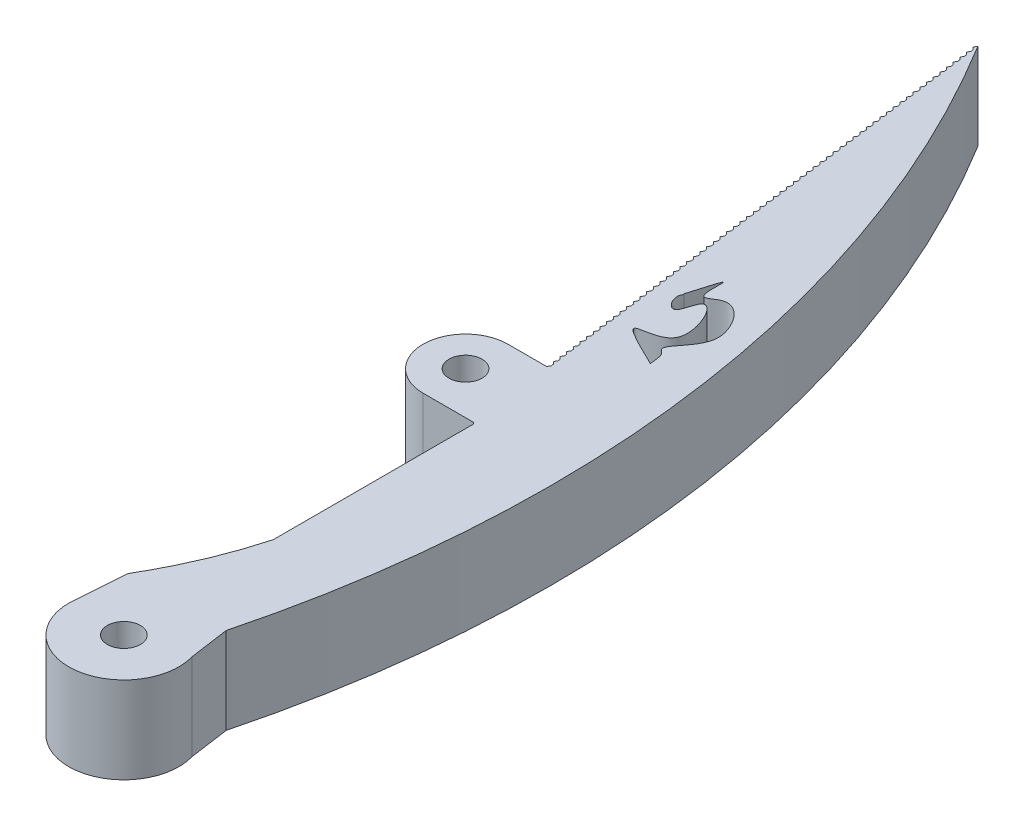
SolidWorks part; units mm, degrees
ref_plane "Front Plane" through (0, 0, 0) normal (0, 0, 1) x (1, 0, 0)
ref_plane "Top Plane" through (0, 0, 0) normal (0, 1, 0) x (1, 0, 0)
ref_plane "Right Plane" through (0, 0, 0) normal (1, 0, 0) x (0, 0, -1)
sketch "Sketch1" plane through (0, 0, 0) normal (0, 1, 0) x (1, 0, 0)
  line L0 (-7.0665, 25.8404) -> (-13.8742, 78.4137)
  line L1 (-7.0665, 38.4137) -> (-7.0665, -14.5937) construction
  line L4 (-2.0665, -1.5863) -> (-1.3548, -6.5863)
  line L5 (-11, -1.5863) -> (-11.3548, -6.5863)
  circle A0 centre (-6.3548, -6.5863) radius 5
  arc A1 (-13.8742, 78.4137) -> (-2.0665, -1.5863) centre (-102.1506, 24.5131) cw
  spline S0 degree 3 poles (-7.0665, 25.8404) (-4.6608, 16.1109) (-5.9719, 6.9687) (-11, -1.5863) knots 0.29583 0.29583 0.29583 0.29583 1 1 1 1
  dimension "D2" = 10
extrude "Boss-Extrude1" add sketch "Sketch1" along normal blind 7.85
sketch "Sketch2" plane through (0, 7.85, 0) normal (0, 1, 0) x (1, 0, 0)
  line L0 (-1.3548, -6.5863) -> (-11.3548, -6.5863) construction
  circle A0 centre (-6.3548, -6.5863) radius 1.5
  dimension "D1" = 3
sketch "Sketch3" plane through (0, 7.85, 0) normal (0, 1, 0) x (1, 0, 0)
  line L0 (-7.0665, 25.8404) -> (-7.2786, 26.0525)
  line L1 (-7.0665, 7.6866) -> (-7.0665, 25.8404) construction
  line L2 (-7.2786, 26.0525) -> (-7.1275, 26.3117)
  line L3 (-7.0665, 25.8404) -> (-7.1275, 26.3117)
  line L4 (-7.0665, 25.8404) -> (-13.8742, 78.4137) construction
  dimension "D1" = 0.3
sketch "Sketch4" plane through (0, 0, 0) normal (0, -1, 0) x (-1, 0, 0)
  line L0 (1.3548, -6.5863) -> (11.3548, -6.5863) construction
  circle A0 centre (6.3548, -6.5863) radius 1.5
  dimension "D1" = 3
extrude "Boss-Extrude9" add sketch "Sketch3" against normal blind 7.5 contours L2 L3 L0
pattern_linear "LPattern1" count 76 spacing 0.7 along (-0.1284, 0, -0.9917) of "Boss-Extrude9"
extrude "Cut-Extrude1" cut sketch "Sketch2" against normal through all contours A0
sketch "Sketch10" plane through (0, 0, 0) normal (0, -1, 0) x (1, 0, 0)
  spline S0 degree 3 poles (-3.7961, -38.6108) (-10.715, -41.9083) (-1.8362, -38.721) (-6.2564, -47.8465) (-6.6902, -42.8482) (-8.1696, -44.9623) (-7.6725, -45.5915) (-7.7718, -45.5603) knots 0 0 0 0 0.43333 0.726209 0.863353 0.989851 1 1 1 1
  spline S1 degree 3 poles (-3.7961, -38.6108) (-3.8737, -39.0877) (-3.821, -39.8269) (-4.7067, -40.3686) (-3.1256, -42.195) (-2.1354, -44.2463) (-4.6923, -47.8436) (-7.63, -44.9948) (-6.1865, -51.1901) (-7.7718, -45.5603) knots 0 0 0 0 0.107517 0.111296 0.210604 0.423358 0.673552 0.750062 1 1 1 1
extrude "Cut-Extrude3" cut sketch "Sketch10" against normal blind 10
sketch "Sketch11" plane through (0, 7.85, 0) normal (0, 1, 0) x (1, 0, 0)
  line L1 (1.2701, 25.9815) -> (-11.779, 25.9815)
  line L3 (0.8736, 33.6794) -> (-11.779, 33.6794)
  arc A0 (-2.0665, -1.5863) -> (-13.8742, 78.4137) centre (-102.1506, 24.5131) ccw construction
  arc A1 (-11.779, 33.6794) -> (-11.779, 25.9815) centre (-11.779, 29.8305) ccw
  arc A2 (-2.0665, -1.5863) -> (-13.8742, 78.4137) centre (-102.1506, 24.5131) ccw
  circle A3 centre (-11.779, 29.8305) radius 1.5
  dimension "D1" = 3
extrude "Boss-Extrude10" add sketch "Sketch11" against normal blind 7.5 contours L1 A2 L3 A1 A3
